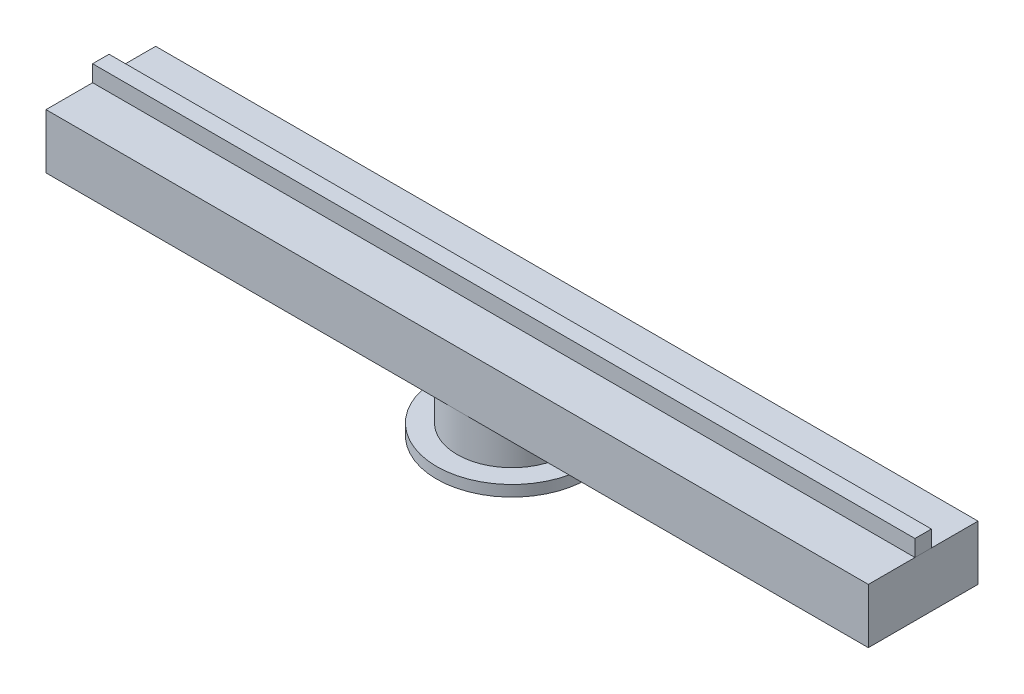
SolidWorks part; units mm, degrees
ref_plane "Plano frontal" through (0, 0, 0) normal (0, 0, 1) x (1, 0, 0)
ref_plane "Plano superior" through (0, 0, 0) normal (0, 1, 0) x (1, 0, 0)
ref_plane "Plano direito" through (0, 0, 0) normal (1, 0, 0) x (0, 0, -1)
sketch "Esboço1" plane through (0, 0, 0) normal (0, 0, 1) x (1, 0, 0)
  line L0 (-750, 0) -> (-750, 100)
  line L1 (-750, 100) -> (750, 100)
  line L2 (750, 100) -> (750, 0)
  line L3 (750, 0) -> (-750, 0)
  point P4 (0, 0)
  dimension "D1" = 100
  dimension "D2" = 1500
extrude "Ressalto-extrusão1" add sketch "Esboço1" along normal mid plane 200
sketch "Esboço3" plane through (0, 0, 0) normal (0, 0, 1) x (1, 0, 0)
  line L0 (-750, 100) -> (-750, 130)
  line L1 (-750, 130) -> (750, 130)
  line L2 (750, 130) -> (750, 100)
  line L3 (750, 100) -> (-750, 100)
  dimension "D1" = 30
extrude "Ressalto-extrusão3" add sketch "Esboço3" along normal mid plane 30 separate body
sketch "Esboço6" plane through (0, 0, 0) normal (0, 0, 1) x (1, 0, 0)
  line L0 (0, 0) -> (0, -602.0344) construction
  line L1 (0, 0) -> (100, 0)
  line L2 (-750, 0) -> (750, 0) construction
  line L3 (100, 0) -> (100, -70)
  line L4 (100, -70) -> (137.5, -70)
  line L5 (137.5, -70) -> (137.5, -90)
  line L6 (137.5, -90) -> (0, -90)
  line L7 (0, -90) -> (0, 0)
  dimension "D1" = 200
  dimension "D2" = 275
  dimension "D3" = 20
  dimension "D4" = 70
revolve "Revolução1" add sketch "Esboço6" angle 360 about L0
sketch "Esboço5" plane through (0, 0, 0) normal (1, 0, 0) x (0, 0, -1)
  line L0 (-100, -10) -> (-145, -10)
  line L2 (-160, -25) -> (-160, -45)
  line L3 (-160, -35) -> (-100, -35) construction
  line L4 (-100, -10) -> (-100, -60)
  line L5 (-100, -60) -> (-145, -60)
  line L6 (-100, 0) -> (-100, -70) construction
  circle A0 centre (-145, -35) radius 6
  arc A1 (-145, -60) -> (-160, -45) centre (-145, -45) cw
  arc A2 (-145, -10) -> (-160, -25) centre (-145, -25) ccw
  point P12 (-160, -60)
  point P15 (-160, -10)
  dimension "D4" = 12
  dimension "D5" = 15
  dimension "D1" = 60
  dimension "D2" = 50
  dimension "D3" = 45
extrude "Ressalto-extrusão5" [suppressed] add sketch "Esboço5" along normal mid plane 10 separate body
pattern_circular "PadrãoCircular4" [suppressed] count 2 every 45
pattern_circular "PadrãoCircular5" [suppressed] count 2 every 45
sketch "Esboço7" plane through (0, 0, 0) normal (0, 0, 1) x (1, 0, 0)
  line L0 (0, 0) -> (0, -646.7179) construction
  line L1 (137.5, -90) -> (137.5, -110)
  line L2 (137.5, -110) -> (107.5, -110)
  line L3 (107.5, -110) -> (107.5, -290)
  line L4 (107.5, -290) -> (0, -290)
  line L5 (0, -290) -> (0, -90)
  line L6 (-137.5, -90) -> (137.5, -90) construction
  line L7 (0, -90) -> (137.5, -90)
  dimension "D1" = 215
  dimension "D2" = 20
  dimension "D3" = 200
revolve "Revolução2" [suppressed] add sketch "Esboço7" angle 360 about L0
sketch "Esboço8" plane through (0, 0, 0) normal (0, 0, 1) x (1, 0, 0)
  line L0 (725, 0) -> (725, -40)
  line L1 (0, 0) -> (750, 0) construction
  line L2 (705, -60) -> (695, -60)
  line L3 (675, -40) -> (675, 0)
  line L4 (675, 0) -> (725, 0)
  line L5 (750, 0) -> (750, 100) construction
  line L6 (0, 0) -> (0, -302.0297) construction
  line L7 (-675, 0) -> (-725, 0)
  line L8 (-675, -40) -> (-675, 0)
  line L9 (-705, -60) -> (-695, -60)
  line L10 (-725, 0) -> (-725, -40)
  circle A0 centre (700, -45) radius 6
  arc A1 (725, -40) -> (705, -60) centre (705, -40) cw
  arc A2 (695, -60) -> (675, -40) centre (695, -40) cw
  arc A3 (-695, -60) -> (-675, -40) centre (-695, -40) ccw
  arc A4 (-725, -40) -> (-705, -60) centre (-705, -40) ccw
  circle A5 centre (-700, -45) radius 6
  point P8 (700, -60)
  point P13 (725, -60)
  point P16 (675, -60)
  point P30 (-675, -60)
  point P31 (-725, -60)
  dimension "D1" = 12
  dimension "D6" = 20
  dimension "D2" = 60
  dimension "D3" = 50
  dimension "D4" = 45
  dimension "D5" = 25
extrude "Ressalto-extrusão6" [suppressed] add sketch "Esboço8" along normal blind 10 separate body
